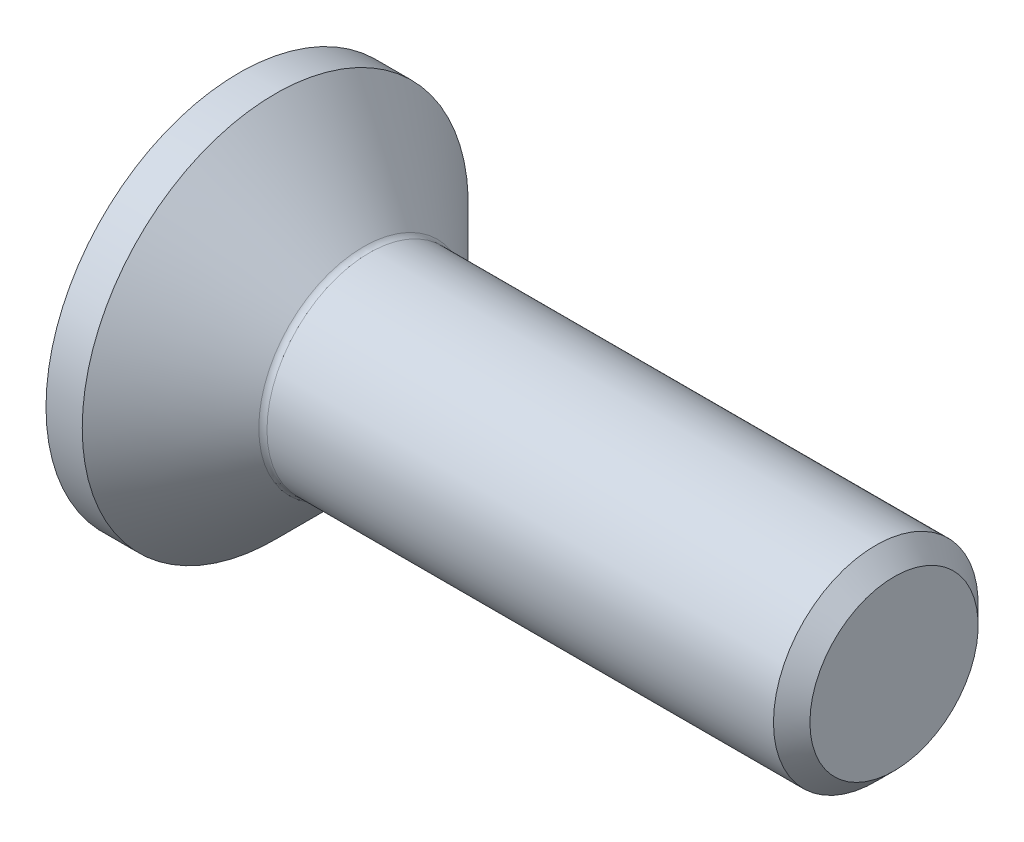
SolidWorks part; units mm, degrees
ref_plane "Plane1" through (0, 0, 0) normal (0, 0, 1) x (1, 0, 0)
ref_plane "Plane2" through (0, 0, 0) normal (0, 1, 0) x (1, 0, 0)
ref_plane "Plane3" through (0, 0, 0) normal (1, 0, 0) x (0, 0, -1)
sketch "BodySke" plane through (0, 0, 0) normal (0, 0, 1) x (1, 0, 0)
  line L0 (0, 0) -> (0, 4.715)
  line L1 (0.885, 4.715) -> (3.1, 2.5)
  line L2 (0, 4.715) -> (0.885, 4.715)
  line L3 (3.1, 2.5) -> (15.555, 2.5)
  line L4 (16, 2.055) -> (16, 0)
  line L5 (16, 0) -> (0, 0)
  line L6 (0, 0) -> (127, 0) construction
  line L7 (0.885, -4.715) -> (3.1, -2.5) construction
  line L8 (16, 2.055) -> (15.555, 2.5)
  line L9 (0, -4.715) -> (0.885, -4.715) construction
  line L10 (16, -2.055) -> (15.555, -2.5) construction
  line L11 (3.9, 8.85) -> (3.9, -13.375) construction
  line L12 (0, 19.05) -> (0, -3.175) construction
  dimension "D1" = 0.885
  dimension "Diameter" = 5
  dimension "Head_ht" = 3.1
  dimension "Length" = 16
  dimension "Body_ch_ang" = 45
  dimension "Head_dia" = 9.43
  dimension "Minor_dia" = 4.11
  dimension "Head_ang" = 90
  dimension "Advance" = 0.8
  dimension "Thread_nom" = 16
revolve "BaseBody" add sketch "BodySke"
cosmetic thread "ThreadCosmetic" [suppressed]
fillet "Fillet1" radius 0.2 1 edges at (3.1, 0, 2.5)
sketch "Sketch2" plane through (0, 0, 0) normal (0, 0, 1) x (1, 0, 0)
  line L0 (0, 1.5) -> (1.9, 1.5)
  line L1 (1.9, 1.5) -> (2.766, 0)
  line L2 (0, 0) -> (127, 0) construction
  line L3 (2.766, 0) -> (0, 0)
  line L4 (0, 0) -> (0, 1.5)
  line L5 (0, -1.5) -> (1.9, -1.5) construction
  line L6 (0, 0) -> (47.625, 0) construction
  line L8 (0, 4.715) -> (0, -4.715) construction
  dimension "D2" = 60
  dimension "PreBroach_depth" = 1.9
  dimension "PreBroach_dia" = 3
revolve "PreBroach" cut sketch "Sketch2" angle 360 about L6
sketch "Sketch3" plane through (0, 0, 0) normal (-1, 0, 0) x (0, 0, 1)
  line L0 (-1.5, -0.866) -> (-1.5, 0.866)
  line L1 (-1.5, 0.866) -> (0, 1.7321)
  line L2 (0, 1.7321) -> (1.5, 0.866)
  line L3 (1.5, 0.866) -> (1.5, -0.866)
  line L4 (1.5, -0.866) -> (0, -1.7321)
  line L5 (0, -1.7321) -> (-1.5, -0.866)
  dimension "D1" = 1.5
  dimension "D2" = 1.5
  dimension "D3" = 3
  dimension "Hex_size" = 3
extrude "Hex" cut sketch "Sketch3" against normal blind 1.9
sketch "ThdSchSke" [suppressed] plane through (0, 0, 0) normal (0, 0, 1) x (1, 0, 0)
  line L0 (17.66, -8.626) -> (16.6979, -10)
  line L1 (17.66, -8.626) -> (18.6221, -10)
  line L2 (18.6221, -10) -> (18.6221, -12.5)
  line L3 (-3.175, 0) -> (5.1513, 0) construction
  line L4 (0, 18.025) -> (0, -18.025) construction
  line L5 (18.6221, -12.5) -> (16.6979, -12.5)
  line L6 (16.6979, -12.5) -> (16.6979, -10)
  dimension "Thread_minor" = 4.11
  dimension "Diameter" = 5
  dimension "Start" = 5.5
  dimension "SideAngle" = 55
  dimension "VeeAngle" = 70
  dimension "Overcut" = 6.25
revolve "ThreadSchematic" [suppressed] cut sketch "ThdSchSke" angle 360 about L3
pattern_linear "ThdSchPat" [suppressed]
equation "\"Thread_minor@ThreadCosmetic\"  =  \"Minor_dia@BodySke\""
equation "\"D1@Sketch3\" = \"Hex_size@Sketch3\" / 2"
equation "\"D2@Sketch3\" = \"D1@Sketch3\""
equation "\"D3@Sketch3\" = \"Hex_size@Sketch3\""
equation "\"Thread_length@ThreadCosmetic\" = ((sgn( (\"Length@BodySke\" - \"Advance@BodySke\" * 3.0 - \"Head_ht@BodySke\" ) - \"Thread_nom@BodySke\" )-1)*( (\"Length@BodySke\" - \"Advance@BodySke\" * 3.0 - \"Head_ht@BodySke\" ) - \"Thread_nom@BodySke\" ))/-2+ \"Thread_nom@BodySke\""
equation "\"Thread_minor@ThdSchSke\" = \"Minor_dia@BodySke\""
equation "\"Diameter@ThdSchSke\" = \"Diameter@BodySke\""
equation "\"Overcut@ThdSchSke\" = \"Diameter@BodySke\" * 1.25"
equation "\"Start@ThdSchSke\" = 0.000001 + \"Length@BodySke\" - \"Thread_length@ThreadCosmetic\"  '---Countersunk---"
equation "\"Num_threads@ThdSchPat\" = int( \"Thread_length@ThreadCosmetic\" / \"Advance@BodySke\" + 0.999 )  + 1"
equation "\"Advance@ThdSchPat\" = \"Thread_length@ThreadCosmetic\" /  (\"Num_threads@ThdSchPat\" - 1) 'relax it"
equation "\"Num_threads@ThdSchPat\" = \"Num_threads@ThdSchPat\" - sgn( \"Num_threads@ThdSchPat\" - 1) '---chamfered tips only---"
